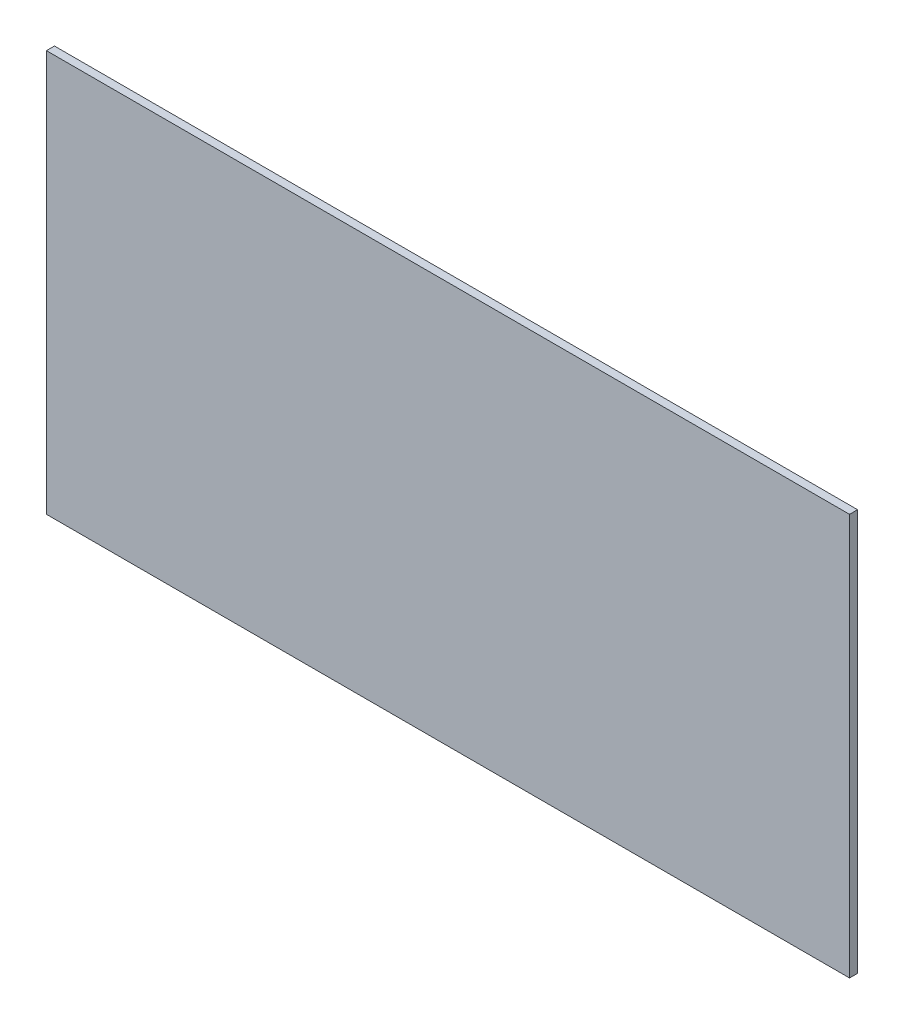
SolidWorks part; units mm, degrees
material "Balsa"
ref_plane "Front Plane" through (0, 0, 0) normal (0, 0, 1) x (1, 0, 0)
ref_plane "Top Plane" through (0, 0, 0) normal (0, 1, 0) x (1, 0, 0)
ref_plane "Right Plane" through (0, 0, 0) normal (1, 0, 0) x (0, 0, -1)
sketch "Sketch1" plane through (0, 0, 0) normal (0, 0, 1) x (1, 0, 0)
  line L1 (400, 200) -> (0, 200)
  line L2 (400, 200) -> (400, 0)
  line L3 (400, 0) -> (0, 0)
  line L4 (0, 200) -> (0, 0)
  dimension "D1" = 400
  dimension "D2" = 200
extrude "Boss-Extrude1" add sketch "Sketch1" along normal blind 4
